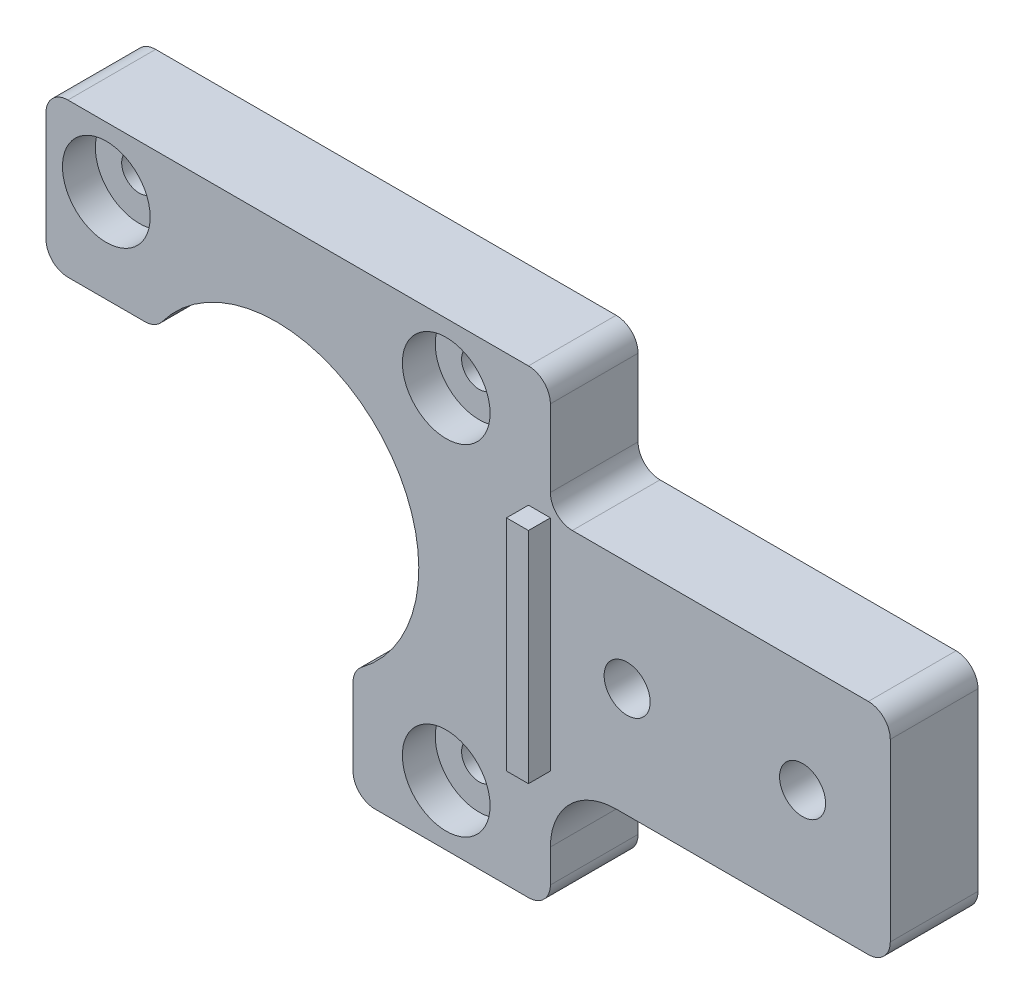
SolidWorks part; units mm, degrees
ref_plane "Plan de face" through (0, 0, 0) normal (0, 0, 1) x (1, 0, 0)
ref_plane "Plan de dessus" through (0, 0, 0) normal (0, 1, 0) x (1, 0, 0)
ref_plane "Plan de droite" through (0, 0, 0) normal (1, 0, 0) x (0, 0, -1)
sketch "Esquisse1" plane through (0, 0, 0) normal (0, 0, 1) x (1, 0, 0)
  line L1 (0, 0) -> (77, 0)
  line L2 (0, 0) -> (0, 42)
  line L3 (0, 42) -> (77, 42)
  line L4 (77, 0) -> (77, 42)
  dimension "D1" = 42
  dimension "D2" = 77
extrude "Boss.-Extru.1" add sketch "Esquisse1" along normal blind 8
sketch "Esquisse3" plane through (0, 0, 8) normal (0, 0, 1) x (1, 0, 0)
  line L0 (42, 42) -> (42, 0) construction
  line L1 (77, 42) -> (0, 42) construction
  line L2 (0, 0) -> (77, 0) construction
  line L3 (0, 42) -> (0, 0) construction
  circle A0 centre (5.5, 36.5) radius 4
  circle A1 centre (36.5, 36.5) radius 4
  circle A2 centre (36.5, 5.5) radius 4
  dimension "D2" = 8
  dimension "D3" = 8
  dimension "D4" = 8
  dimension "D1" = 42
  dimension "D5" = 5.5
  dimension "D6" = 5.5
  dimension "D7" = 5.5
  dimension "D8" = 5.5
  dimension "D9" = 5.5
  dimension "D10" = 5.5
extrude "Enlèv. mat.-Extru.1" cut sketch "Esquisse3" against normal blind 3
sketch "Esquisse4" plane through (0, 0, 8) normal (0, 0, 1) x (1, 0, 0)
  line L0 (0, 42) -> (0, 0) construction
  line L1 (77, 42) -> (0, 42) construction
  circle A0 centre (21, 21) radius 13
  dimension "D1" = 26
  dimension "D2" = 21
  dimension "D3" = 21
extrude "Enlèv. mat.-Extru.2" cut sketch "Esquisse4" against normal through all
sketch "Esquisse5" plane through (0, 0, 8) normal (0, 0, 1) x (1, 0, 0)
  line L1 (0, 0) -> (28, 0)
  line L2 (0, 0) -> (0, 28)
  line L3 (0, 28) -> (28, 28)
  line L4 (28, 0) -> (28, 28)
  dimension "D1" = 28
  dimension "D2" = 28
extrude "Enlèv. mat.-Extru.3" cut sketch "Esquisse5" against normal through all
sketch "Esquisse10" plane through (0, 0, 5) normal (0, 0, 1) x (1, 0, 0)
  circle A0 centre (5.5, 36.5) radius 1.6
  circle A1 centre (36.5, 36.5) radius 1.6
  circle A2 centre (36.5, 5.5) radius 1.6
  dimension "D1" = 3.2
  dimension "D2" = 3.2
  dimension "D3" = 3.2
extrude "Enlèv. mat.-Extru.4" cut sketch "Esquisse10" against normal through all
sketch "Esquisse11" plane through (0, 0, 8) normal (0, 0, 1) x (1, 0, 0)
  line L0 (28, 0) -> (28, 10.0455) construction
  line L1 (77, 0) -> (46, 0)
  line L2 (77, 0) -> (77, 11)
  line L3 (77, 11) -> (46, 11)
  line L4 (46, 0) -> (46, 11)
  line L7 (77, 42) -> (46, 42)
  line L8 (77, 42) -> (77, 31)
  line L9 (77, 31) -> (46, 31)
  line L10 (46, 42) -> (46, 31)
  dimension "D1" = 18
  dimension "D2" = 11
  dimension "D3" = 11
  dimension "D4" = 18
extrude "Enlèv. mat.-Extru.5" cut sketch "Esquisse11" against normal through all
sketch "Esquisse12" plane through (0, 0, 8) normal (0, 0, 1) x (1, 0, 0)
  line L0 (46, 42) -> (0, 42) construction
  line L1 (77, 11) -> (77, 31) construction
  circle A0 centre (53, 21) radius 2.1
  circle A1 centre (69, 21) radius 2.1
  dimension "D1" = 4.2
  dimension "D2" = 4.2
  dimension "D3" = 21
  dimension "D4" = 21
  dimension "D5" = 8
  dimension "D6" = 16
extrude "Enlèv. mat.-Extru.6" cut sketch "Esquisse12" against normal through all
fillet "Congé1" radius 6 1 edges at (46, 11, 4)
fillet "Congé2" radius 2 10 edges at (28, 10.0455, 4) (0, 42, 4) (77, 11, 4) (10.0455, 28, 4) (0, 28, 4) (28, 0, 4) (46, 0, 4) (46, 42, 4) (46, 31, 4) (77, 31, 4)
sketch "Sketch1" plane through (0, 0, 8) normal (0, 0, 1) x (1, 0, 0)
  line L0 (46, 40) -> (46, 5) construction
  line L1 (48, 31) -> (75, 31) construction
  line L2 (46, 11) -> (44, 11)
  line L3 (46, 11) -> (46, 31)
  line L4 (46, 31) -> (44, 31)
  line L5 (44, 11) -> (44, 31)
  dimension "D1" = 20
  dimension "D2" = 2
extrude "Boss-Extrude1" add sketch "Sketch1" along normal blind 2
